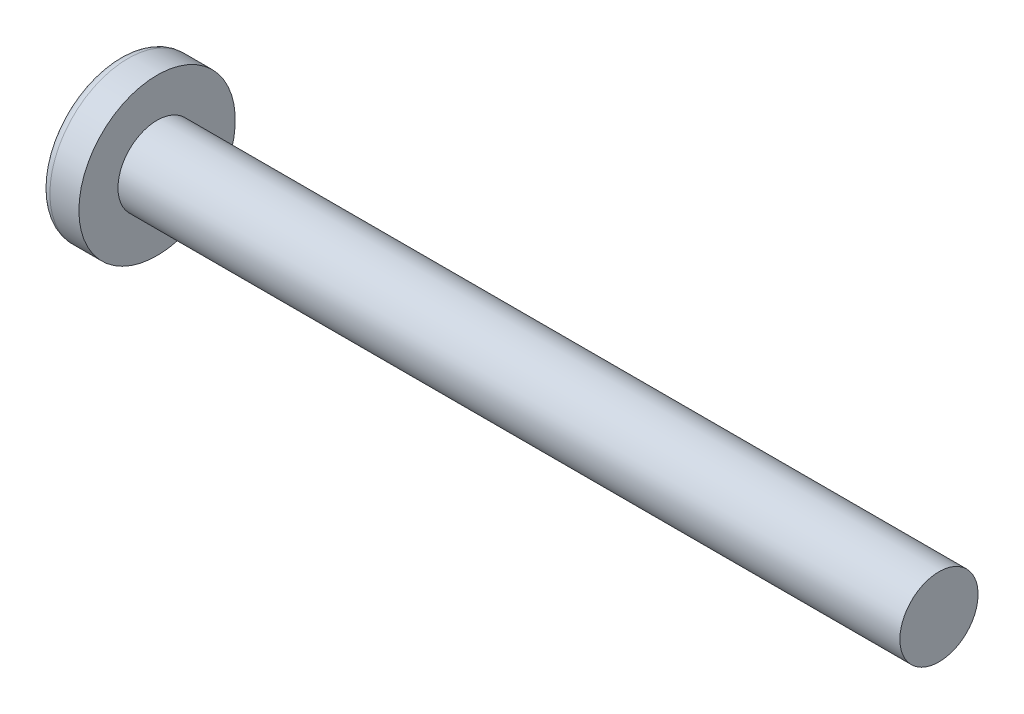
SolidWorks part; units mm, degrees
ref_plane "Plane1" through (0, 0, 0) normal (0, 0, 1) x (1, 0, 0)
ref_plane "Plane2" through (0, 0, 0) normal (0, 1, 0) x (1, 0, 0)
ref_plane "Plane3" through (0, 0, 0) normal (1, 0, 0) x (0, 0, -1)
other "Configuration Table"
sketch "BodySke" plane through (0, 0, 0) normal (0, 0, 1) x (1, 0, 0)
  line L0 (3.1, 2) -> (3.1, 4)
  line L1 (3.8, 6.35) -> (3.8, -3.175) construction
  line L2 (-25.4, 0) -> (127, 0) construction
  line L3 (43.1, 0) -> (0, 0)
  line L4 (3.1, 2) -> (43.1, 2)
  line L5 (43.1, 2) -> (43.1, 0)
  line L6 (1.6164, 4) -> (3.1, 4)
  line L7 (3.1, -2) -> (43.1, -2) construction
  line L8 (3.1, 6.35) -> (3.1, -3.175) construction
  arc A0 (1.227, 3.8007) -> (0, 0) centre (6.5, 0) ccw
  arc A2 (1.227, 3.8007) -> (1.6164, 4) centre (1.6164, 3.52) cw
  dimension "Head_crown_rad" = 6.5
  dimension "Head_fillet_rad" = 0.48
  dimension "Diameter" = 4
  dimension "Length" = 40
  dimension "Head_ht" = 3.1
  dimension "Head_dia" = 8
  dimension "Advance" = 0.7
  dimension "Thread_nom" = 40
revolve "Base-Revolve" add sketch "BodySke" angle 360 about L2
cosmetic thread "ThreadCosmetic" [suppressed] parameters "Thread_length"=39.3, "Thread_minor"=3.22
sketch "Sketch3" plane through (0, 0, 0) normal (1, 0, 0) x (0, 0, -1)
  line L0 (0.465, -2.2) -> (-0.465, -2.2)
  line L1 (0.465, -2.2) -> (0.465, 2.2)
  line L2 (-0.465, 2.2) -> (0.465, 2.2)
  line L3 (-0.465, 2.2) -> (-0.465, -2.2)
  dimension "Cross_dia" = 4.4
  dimension "D1" = 2.2
  dimension "Cross_width" = 0.93
  dimension "D2" = 0.465
ref_plane "Plane4" through (2.45, 0, 0) normal (1, 0, 0) x (0, 0, -1)
sketch "Sketch4" plane through (2.45, 0, 0) normal (1, 0, 0) x (0, 0, -1)
  line L0 (0.2325, -0.2325) -> (-0.2325, -0.2325)
  line L1 (0.2325, -0.2325) -> (0.2325, 0.2325)
  line L2 (-0.2325, 0.2325) -> (0.2325, 0.2325)
  line L3 (-0.2325, 0.2325) -> (-0.2325, -0.2325)
  dimension "D2" = 0.465
  dimension "D1" = 0.465
  dimension "D3" = 0.2325
  dimension "D4" = 0.2325
loft "Cut-Loft1" cut profiles "Sketch3", "Sketch4"
pattern_circular "CirPattern1" count 2 every 90 about axis through (0, 0, 0) along (1, 0, 0) of "Cut-Loft1"
sketch "ThdSchSke" plane through (0, 0, 0) normal (0, 0, 1) x (1, 0, 0)
  line L0 (3.8, -1.61) -> (3.5269, -2)
  line L1 (3.8, -1.61) -> (4.0731, -2)
  line L2 (4.0731, -2) -> (4.0731, -2.5)
  line L3 (-3.175, 0) -> (5.1513, 0) construction
  line L5 (4.0731, -2.5) -> (3.5269, -2.5)
  line L6 (3.5269, -2.5) -> (3.5269, -2)
  dimension "Diameter" = 4
  dimension "SideAngle" = 55
  dimension "VeeAngle" = 70
  dimension "Thread_minor" = 3.22
  dimension "Overcut" = 5
  dimension "Start" = 3.8
revolve "ThreadSchematic" [suppressed] cut sketch "ThdSchSke" angle 360 about L3
pattern_linear "ThdSchPat" [suppressed]
equation "\"D1@Sketch3\" = \"Cross_dia@Sketch3\" / 2"
equation "\"D2@Sketch3\" = \"Cross_width@Sketch3\" / 2"
equation "\"D1@Sketch4\" = \"Cross_width@Sketch3\" *.5"
equation "\"D2@Sketch4\" = \"D1@Sketch4\""
equation "\"D3@Sketch4\" = \"D1@Sketch4\" / 2"
equation "\"D4@Sketch4\" = \"D2@Sketch4\" / 2"
equation "\"Thread_length@ThreadCosmetic\" = ((sgn( (\"Length@BodySke\" - \"Advance@BodySke\" ) - \"Thread_nom@BodySke\" )-1)*( (\"Length@BodySke\" - \"Advance@BodySke\" ) - \"Thread_nom@BodySke\" ))/-2+ \"Thread_nom@BodySke\""
equation "\"Thread_minor@ThdSchSke\" = \"Thread_minor@ThreadCosmetic\""
equation "\"Diameter@ThdSchSke\" = \"Diameter@BodySke\""
equation "\"Overcut@ThdSchSke\" = \"Diameter@BodySke\" * 1.25"
equation "\"Start@ThdSchSke\" = \"Head_ht@BodySke\" + \"Length@BodySke\" - \"Thread_length@ThreadCosmetic\"  '---Non-countersunk---"
equation "\"Num_threads@ThdSchPat\" = int( \"Thread_length@ThreadCosmetic\" / \"Advance@BodySke\" + 0.999 )  + 1"
equation "\"Advance@ThdSchPat\" = \"Thread_length@ThreadCosmetic\" /  (\"Num_threads@ThdSchPat\" - 1) 'relax it"
